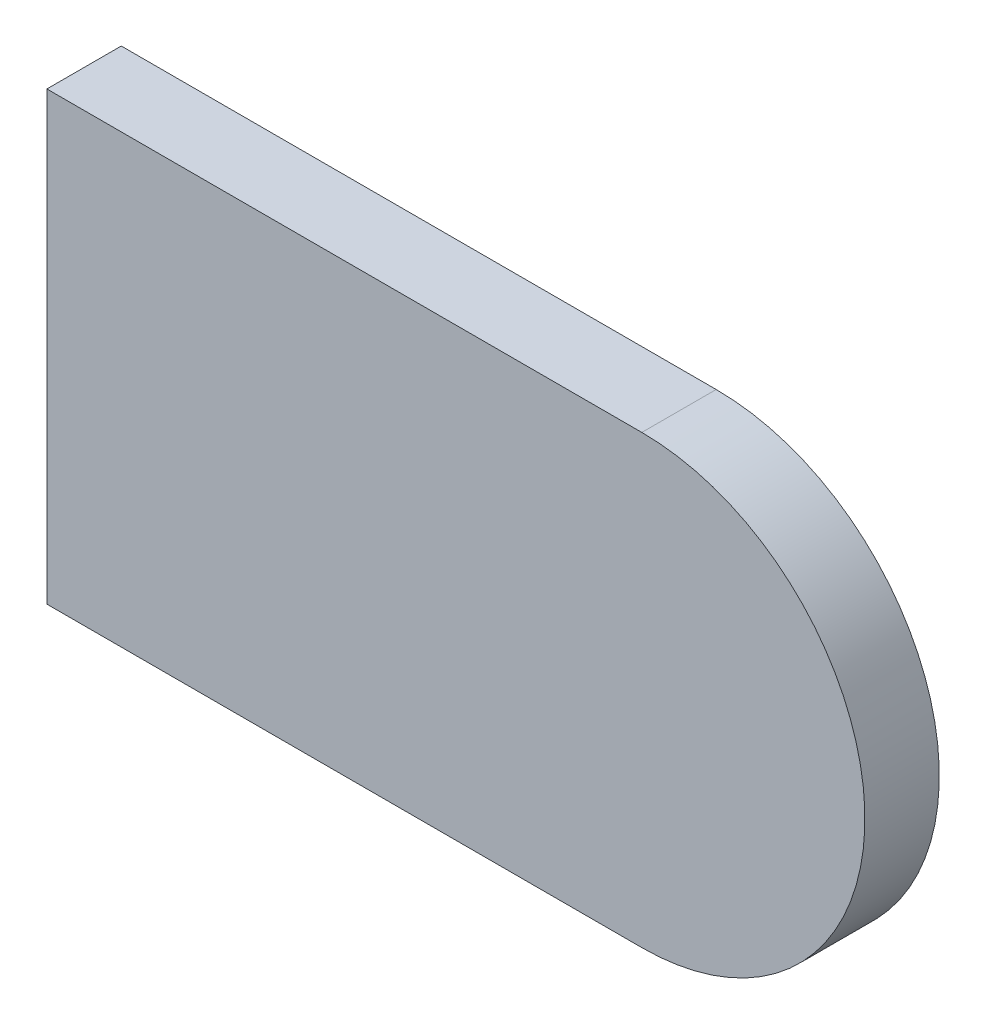
SolidWorks part; units mm, degrees
material "Plain Carbon Steel"
ref_plane "Front Plane" through (0, 0, 0) normal (0, 0, 1) x (1, 0, 0)
ref_plane "Top Plane" through (0, 0, 0) normal (0, 1, 0) x (1, 0, 0)
ref_plane "Right Plane" through (0, 0, 0) normal (1, 0, 0) x (0, 0, -1)
sketch "Sketch1" plane through (0, 0, 0) normal (0, 0, 1) x (1, 0, 0)
  line L1 (0, 0) -> (80, 0)
  line L2 (0, 0) -> (0, -60)
  line L3 (0, -60) -> (80, -60)
  arc A0 (80, 0) -> (80, -60) centre (80, -30) cw
  dimension "D2" = 30
  dimension "D1" = 80
extrude "Boss-Extrude1" add sketch "Sketch1" along normal blind 10
